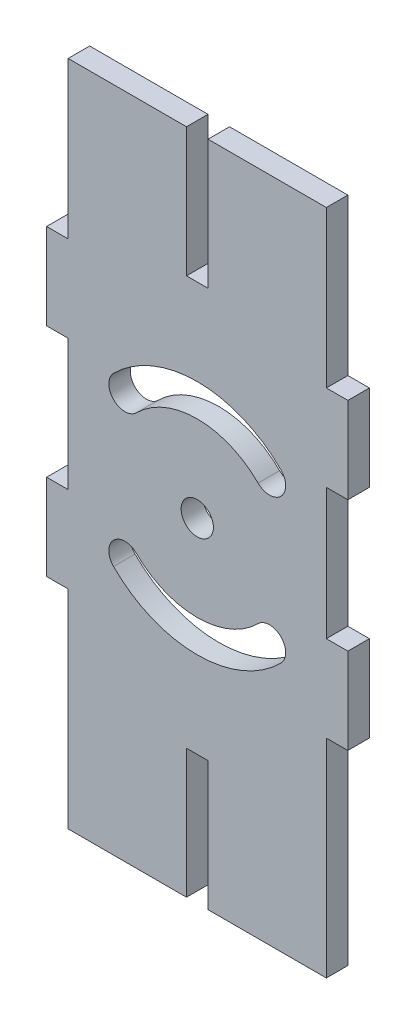
SolidWorks part; units mm, degrees
ref_plane "Front Plane" through (0, 0, 0) normal (0, 0, 1) x (1, 0, 0)
ref_plane "Top Plane" through (0, 0, 0) normal (0, 1, 0) x (1, 0, 0)
ref_plane "Right Plane" through (0, 0, 0) normal (1, 0, 0) x (0, 0, -1)
sketch "Sketch1" plane through (0, 0, 0) normal (0, 0, 1) x (1, 0, 0)
  line L0 (-17.4625, 365.7785) -> (-17.4625, 346.7285) construction
  line L1 (-38.1, 365.7785) -> (-20.6375, 365.7785)
  line L2 (-38.1, 365.7785) -> (-38.1, 267.3188)
  line L3 (-38.1, 267.3188) -> (-20.6375, 267.3188)
  line L4 (0, 365.7785) -> (0, 267.3188)
  line L5 (-17.4625, 267.3188) -> (0, 267.3188)
  line L6 (-20.6375, 365.7785) -> (-20.6375, 346.7285)
  line L7 (-20.6375, 346.7285) -> (-17.4625, 346.7285)
  line L8 (-17.4625, 365.7785) -> (-17.4625, 346.7285)
  line L9 (-3.175, 267.3188) -> (-34.925, 267.3188) construction
  line L11 (-20.6375, 267.3188) -> (-20.6375, 286.3688)
  line L12 (-20.6375, 286.3688) -> (-17.4625, 286.3688)
  line L13 (-17.4625, 267.3188) -> (-17.4625, 286.3688)
  line L14 (-17.4625, 365.7785) -> (0, 365.7785)
  dimension "D1" = 19.05
  dimension "D2" = 19.05
extrude "Boss-Extrude1" add sketch "Sketch1" along normal blind 3.175 contours L3 L11 L12 L13 L5 L4 L14 L8 L7 L6 L1 L2
sketch "Sketch3" plane through (0, 0, 3.175) normal (0, 0, 1) x (1, 0, 0)
  line L0 (-19.05, 346.7285) -> (-19.05, 286.3688)
  line L1 (-20.6375, 346.7285) -> (-17.4625, 346.7285) construction
  line L2 (-20.6375, 286.3688) -> (-17.4625, 286.3688) construction
  line L3 (0, 316.5487) -> (-38.1, 316.5487)
  line L4 (0, 365.7785) -> (0, 267.3188) construction
  line L5 (-38.1, 365.7785) -> (-38.1, 267.3188) construction
  line L6 (-8.3859, 327.2127) -> (-29.7141, 305.8846)
  line L7 (-29.7141, 327.2127) -> (-8.3859, 305.8846)
  circle A0 centre (-19.05, 316.5487) radius 2.3813
  arc A1 (-29.7141, 305.8846) -> (-8.3859, 305.8846) centre (-19.05, 316.5487) ccw construction
  arc A2 (-31.3979, 304.2008) -> (-6.7021, 304.2008) centre (-19.05, 316.5487) ccw
  arc A3 (-28.0303, 307.5684) -> (-10.0697, 307.5684) centre (-19.05, 316.5487) ccw
  arc A4 (-28.0303, 307.5684) -> (-31.3979, 304.2008) centre (-29.7141, 305.8846) ccw
  arc A5 (-6.7021, 304.2008) -> (-10.0697, 307.5684) centre (-8.3859, 305.8846) ccw
  arc A6 (-29.7141, 327.2127) -> (-8.3859, 327.2127) centre (-19.05, 316.5487) cw construction
  arc A7 (-6.7021, 328.8965) -> (-31.3979, 328.8965) centre (-19.05, 316.5487) ccw
  arc A8 (-10.0697, 325.5289) -> (-28.0303, 325.5289) centre (-19.05, 316.5487) ccw
  arc A9 (-10.0697, 325.5289) -> (-6.7021, 328.8965) centre (-8.3859, 327.2127) ccw
  arc A10 (-31.3979, 328.8965) -> (-28.0303, 325.5289) centre (-29.7141, 327.2127) ccw
  point P16 (-19.05, 301.4674)
  point P21 (-19.05, 331.6299)
  dimension "D1" = 4.7625
  dimension "D2" = 2.3813
  dimension "D3" = 2.3813
  dimension "D4" = 12.7
  dimension "D5" = 12.7
  dimension "D6" = 90
  dimension "D7" = 45
extrude "Cut-Extrude1" cut sketch "Sketch3" against normal blind 5.08
sketch "Sketch5" plane through (0, 0, 3.175) normal (0, 0, 1) x (1, 0, 0)
  line L0 (0, 365.7785) -> (0, 267.3188) construction
  line L1 (0, 342.7177) -> (3.175, 342.7177)
  line L2 (0, 342.7177) -> (0, 330.0177)
  line L3 (0, 330.0177) -> (3.175, 330.0177)
  line L4 (3.175, 342.7177) -> (3.175, 330.0177)
  line L5 (3.175, 342.7177) -> (0, 342.7177) construction
  line L6 (3.175, 297.9799) -> (0, 297.9799) construction
  line L7 (0, 297.9799) -> (3.175, 297.9799)
  line L8 (0, 297.9799) -> (0, 310.6799)
  line L9 (0, 310.6799) -> (3.175, 310.6799)
  line L10 (3.175, 297.9799) -> (3.175, 310.6799)
  line L11 (-38.1, 365.7785) -> (-38.1, 267.3188) construction
  line L12 (-38.1, 310.6799) -> (-41.275, 310.6799)
  line L13 (-38.1, 310.6799) -> (-38.1, 297.9799)
  line L14 (-38.1, 297.9799) -> (-41.275, 297.9799)
  line L15 (-41.275, 310.6799) -> (-41.275, 297.9799)
  line L16 (-38.1, 342.7177) -> (-41.275, 342.7177) construction
  line L17 (-38.1, 342.7177) -> (-41.275, 342.7177)
  line L18 (-38.1, 342.7177) -> (-38.1, 330.0177)
  line L19 (-38.1, 330.0177) -> (-41.275, 330.0177)
  line L20 (-41.275, 342.7177) -> (-41.275, 330.0177)
  line L21 (-38.1, 310.6799) -> (-41.275, 310.6799) construction
  line L22 (-41.275, 297.9799) -> (-41.275, 310.6799) construction
extrude "Boss-Extrude2" add sketch "Sketch5" against normal blind 3.175
